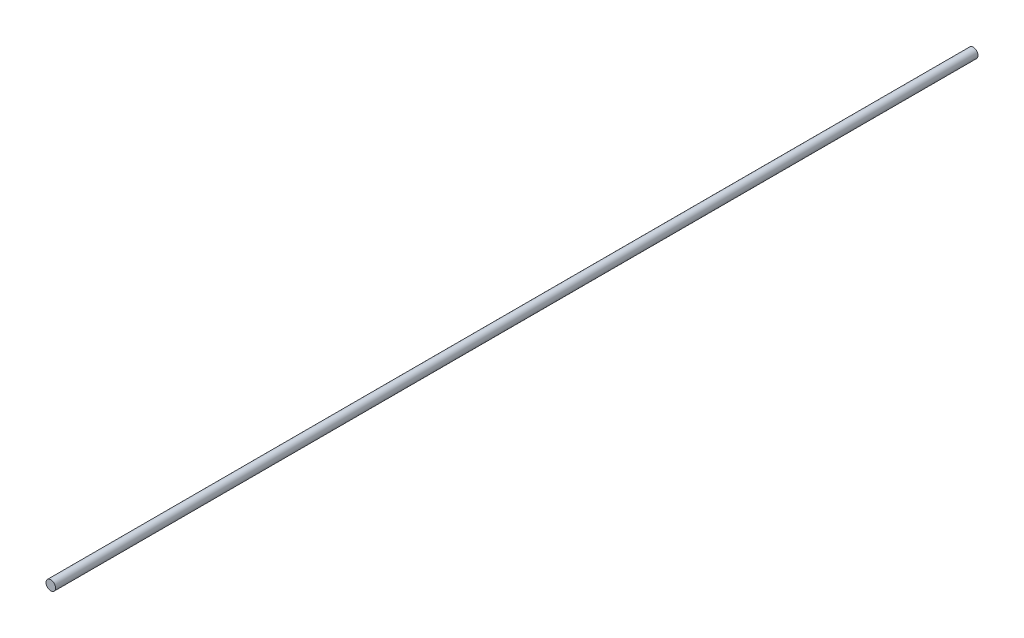
SolidWorks part; units mm, degrees
ref_plane "Front Plane" through (0, 0, 0) normal (0, 0, 1) x (1, 0, 0)
ref_plane "Top Plane" through (0, 0, 0) normal (0, 1, 0) x (1, 0, 0)
ref_plane "Right Plane" through (0, 0, 0) normal (1, 0, 0) x (0, 0, -1)
sketch "Sketch1" plane through (0, 0, 0) normal (0, 0, 1) x (1, 0, 0)
  circle A0 centre (0, 0) radius 4.7625
  dimension "D1" = 9.525
extrude "Boss-Extrude1" add sketch "Sketch1" along normal blind 914.4
